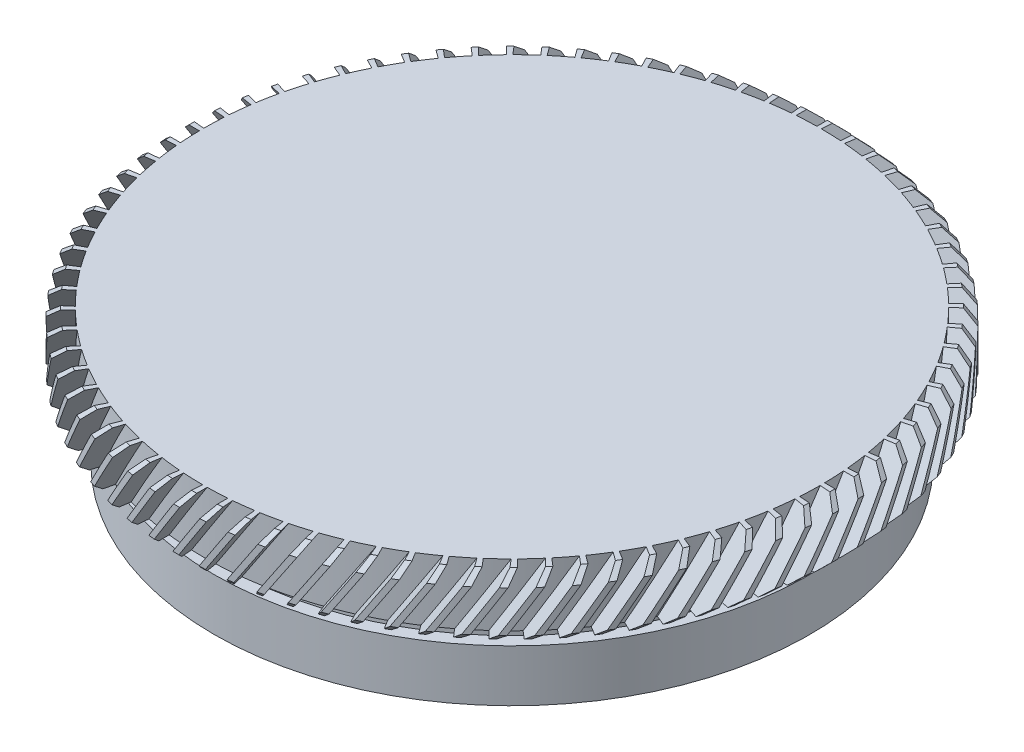
SolidWorks part; units mm, degrees
ref_plane "前视基准面" through (0, 0, 0) normal (0, 0, 1) x (1, 0, 0)
ref_plane "上视基准面" through (0, 0, 0) normal (0, 1, 0) x (1, 0, 0)
ref_plane "右视基准面" through (0, 0, 0) normal (1, 0, 0) x (0, 0, -1)
sketch "草图1" plane through (0, 0, 0) normal (0, 0, 1) x (1, 0, 0)
  line L0 (0, 66.6288) -> (0, -106.6399) construction
  line L1 (-97.6622, 0) -> (93.4292, 0) construction
  line L2 (0, 21.8713) -> (15.875, 21.8713)
  line L3 (15.875, 21.8713) -> (15.875, 18.8713)
  line L4 (13.75, 18.8713) -> (13.75, 17.8713)
  line L5 (13.75, 18.8713) -> (15.875, 18.8713)
  line L6 (14.35, 17.8713) -> (14.35, 15.3713)
  line L7 (13.75, 17.8713) -> (14.35, 17.8713)
  line L8 (12.5, 18.8713) -> (12.5, 15.3713)
  line L9 (0, 21.8713) -> (0, 18.8713)
  line L10 (12.5, 15.3713) -> (14.35, 15.3713)
  line L11 (0, 18.8713) -> (12.5, 18.8713)
  dimension "D1" = 15.875
  dimension "D2" = 3
  dimension "D3" = 13.75
  dimension "D4" = 14.35
  dimension "D5" = 12.5
  dimension "D6" = 1
  dimension "D7" = 2.5
revolve "旋转2" add sketch "草图1" angle 360 about L0
cosmetic thread "装饰螺纹线1" parameters "D2"=28.5
chamfer "倒角1" distance 0.5 angle 45 2 edges at (0, 21.8713, 15.875) (0, 18.8713, 15.875)
sketch "草图2" plane through (0, 0, 0) normal (0, 0, 1) x (1, 0, 0)
  line L0 (1.1082, 23.3033) -> (-5.3395, 13.2735)
  line L1 (1.1082, 23.3033) -> (1.7811, 22.8706)
  line L2 (-5.3395, 13.2735) -> (-4.6666, 12.8409)
  line L3 (1.7811, 22.8706) -> (-4.6666, 12.8409)
  dimension "D1" = 0.8
surface "曲面-等距1" parameters "D1"=1
extrude "切除-拉伸1" cut sketch "草图2" against normal up to surface (15.1663 mm away) from offset 30
delete or keep bodies "实体-删除/保留 1" type delete bodies bodies 107
pattern_circular "阵列(圆周)2" count 80 over 360 about axis through (0, 0, 0) along (0, 1, 0) of "切除-拉伸1"
